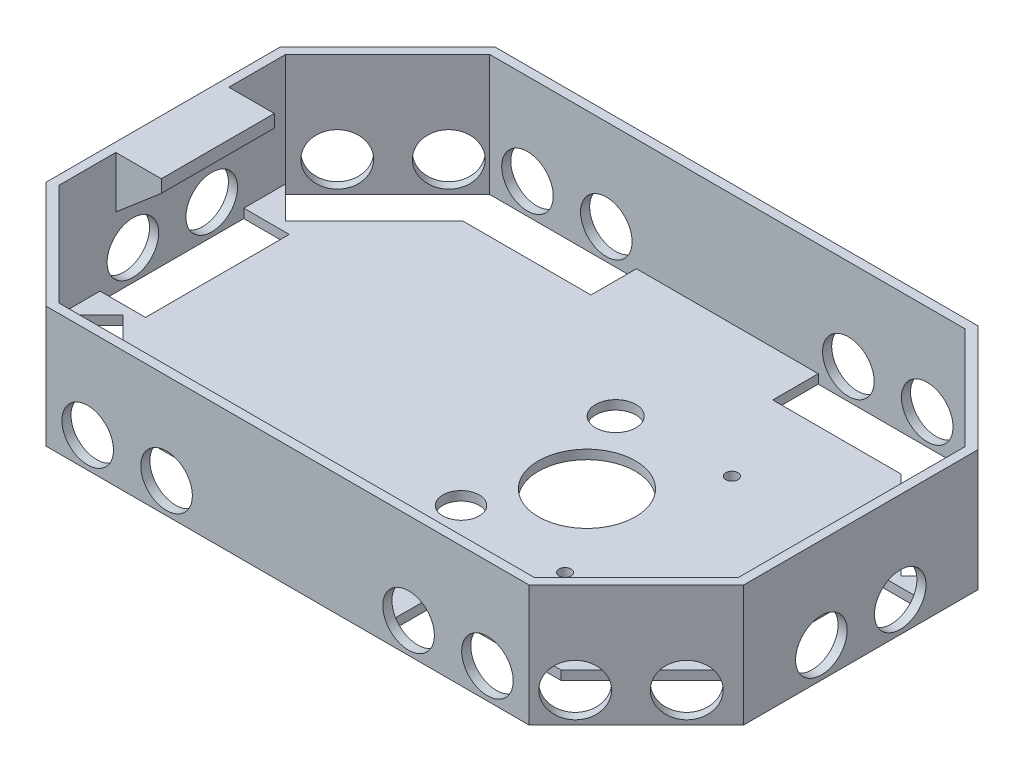
SolidWorks part; units mm, degrees
ref_plane "Front Plane" through (0, 0, 0) normal (0, 0, 1) x (1, 0, 0)
ref_plane "Top Plane" through (0, 0, 0) normal (0, 1, 0) x (1, 0, 0)
ref_plane "Right Plane" through (0, 0, 0) normal (1, 0, 0) x (0, 0, -1)
sketch "Sketch2" plane through (0, 0, 0) normal (0, 1, 0) x (1, 0, 0)
  line L0 (-115, 0) -> (115, 0) construction
  line L1 (-115, -74) -> (115, -74)
  line L2 (-115, -74) -> (-115, 74)
  line L3 (-115, 74) -> (115, 74)
  line L4 (115, -74) -> (115, 74)
  line L5 (-115, -74) -> (115, 74) construction
  line L6 (-115, 74) -> (115, -74) construction
  line L7 (-115, 74) -> (45, 74) construction
  line L8 (45, 74) -> (45, 0) construction
  circle A0 centre (45, 27.5) radius 2
  circle A1 centre (24.698, 0) radius 16
  circle A2 centre (8.698, 25.5) radius 6
  circle A3 centre (45, -27.5) radius 2
  circle A4 centre (8.698, -25.5) radius 6
  point P0 (0, 0)
  point P8 (45, 27.5)
  dimension "D1" = 230
  dimension "D2" = 148
  dimension "D3" = 160
  dimension "D4" = 27.5
extrude "Boss-Extrude1" add sketch "Sketch2" along normal blind 40 contours L2 L1 L4 L3
sketch "Sketch4" plane through (0, 40, 0) normal (0, 1, 0) x (1, 0, 0)
  line L0 (-79.6447, 74) -> (-115, 38.6447)
  line L1 (115, 74) -> (-115, 74) construction
  line L2 (-115, 74) -> (-115, -74) construction
  line L3 (-115, 38.6447) -> (-115, 74)
  line L4 (-115, 74) -> (-79.6447, 74)
  line L5 (-115, 0) -> (115, 0) construction
  line L6 (115, -74) -> (115, 74) construction
  line L7 (115, 0) -> (0, 0) construction
  line L8 (0, 0) -> (0, 74) construction
  line L9 (0, 74) -> (0, -74) construction
  line L10 (-115, -74) -> (115, -74) construction
  line L11 (115, 74) -> (79.6447, 74)
  line L12 (115, 38.6447) -> (115, 74)
  line L13 (79.6447, 74) -> (115, 38.6447)
  line L14 (115, -38.6447) -> (115, -74)
  line L15 (115, -74) -> (79.6447, -74)
  line L16 (79.6447, -74) -> (115, -38.6447)
  line L17 (-115, -74) -> (-79.6447, -74)
  line L18 (-115, -38.6447) -> (-115, -74)
  line L19 (-79.6447, -74) -> (-115, -38.6447)
  dimension "D1" = 50
  dimension "D2" = 159.2893
  dimension "D3" = 77.2893
  dimension "D4" = 230
  dimension "D5" = 148
extrude "Cut-Extrude2" cut sketch "Sketch4" against normal blind 126
shell "Shell2" thickness 3
sketch "Sketch6" plane through (0, 0, 0) normal (0, -1, 0) x (1, 0, 0)
  circle A0 centre (24.698, 0) radius 16
  circle A1 centre (8.698, 25.5) radius 6
  circle A2 centre (45, 27.5) radius 2
  circle A3 centre (8.698, -25.5) radius 6.6581
  circle A4 centre (45, -27.5) radius 2.011
extrude "Cut-Extrude3" cut sketch "Sketch6" against normal blind 126
sketch "Sketch8" plane through (0, 3, 0) normal (0, 1, 0) x (1, 0, 0)
  line L0 (-78.402, 71) -> (78.402, 71) construction
  line L1 (0, 71) -> (0, -71) construction
  line L2 (-75.9393, 71) -> (-29.9737, 71)
  line L4 (-72.1888, 56) -> (-29.9737, 56)
  line L5 (-29.9737, 71) -> (-29.9737, 56)
  line L6 (-78.402, -71) -> (78.402, -71) construction
  line L11 (-115, 0) -> (104.5294, 0) construction
  line L12 (-115, 0) -> (115, 0) construction
  line L21 (112, -37.402) -> (112, 37.402) construction
  line L22 (112, 23.5674) -> (97, 23.5674)
  line L23 (112, 23.5674) -> (112, -23.8324)
  line L24 (112, -23.8324) -> (97, -23.8324)
  line L25 (97, 23.5674) -> (97, -23.8324)
  line L26 (-112, -23.8324) -> (-97, -23.8324)
  line L27 (-97, 23.5674) -> (-97, -23.8324)
  line L28 (-112, 23.5674) -> (-97, 23.5674)
  line L29 (-112, 23.5674) -> (-112, -23.8324)
  line L30 (-78.402, 71) -> (-112, 37.402)
  line L31 (-112, 37.402) -> (-101.3934, 26.7954)
  line L32 (-101.3934, 26.7954) -> (-72.1888, 56)
  line L33 (-78.402, 71) -> (-75.9393, 71)
  line L34 (101.3934, 26.7954) -> (72.1888, 56)
  line L35 (112, 37.402) -> (101.3934, 26.7954)
  line L36 (78.402, 71) -> (112, 37.402)
  line L37 (78.402, 71) -> (75.9393, 71)
  line L38 (75.9393, 71) -> (29.9737, 71)
  line L39 (29.9737, 71) -> (29.9737, 56)
  line L40 (72.1888, 56) -> (29.9737, 56)
  line L41 (112, -37.402) -> (101.3934, -26.7954)
  line L42 (78.402, -71) -> (112, -37.402)
  line L43 (78.402, -71) -> (75.9393, -71)
  line L44 (75.9393, -71) -> (29.9737, -71)
  line L45 (29.9737, -71) -> (29.9737, -56)
  line L46 (72.1888, -56) -> (29.9737, -56)
  line L47 (101.3934, -26.7954) -> (72.1888, -56)
  line L48 (-101.3934, -26.7954) -> (-72.1888, -56)
  line L49 (-112, -37.402) -> (-101.3934, -26.7954)
  line L50 (-78.402, -71) -> (-112, -37.402)
  line L51 (-78.402, -71) -> (-75.9393, -71)
  line L52 (-75.9393, -71) -> (-29.9737, -71)
  line L53 (-29.9737, -71) -> (-29.9737, -56)
  line L54 (-72.1888, -56) -> (-29.9737, -56)
  point P0 (-75.9393, 71)
  point P1 (-29.9737, 71)
  dimension "D2" = 15
extrude "Cut-Extrude4" cut sketch "Sketch8" against normal blind 10
sketch "Sketch10" plane through (0, 0, -74) normal (0, 0, -1) x (-1, 0, 0)
  line L0 (0, 0) -> (0, 40) construction
  line L1 (79.6447, 0) -> (-79.6447, 0) construction
  line L2 (79.6447, 40) -> (-79.6447, 40) construction
  circle A0 centre (-65.902, 10) radius 8.5
  circle A1 centre (-39.902, 10) radius 8.5
  circle A2 centre (39.902, 10) radius 8.5
  circle A3 centre (65.902, 10) radius 8.5
sketch "Sketch12" plane through (0, 0, 74) normal (0, 0, 1) x (1, 0, 0)
  circle A0 centre (-65.902, 10) radius 8.5
  circle A1 centre (-39.902, 10) radius 8.5
  circle A2 centre (39.902, 10) radius 8.5
  circle A3 centre (65.902, 10) radius 8.5
extrude "Cut-Extrude7" cut sketch "Sketch12" along normal blind 4 and the other way blind 13
sketch "Sketch13" plane through (0, 0, -74) normal (0, 0, -1) x (-1, 0, 0)
  circle A0 centre (-39.902, 10) radius 8.5
  circle A1 centre (-65.902, 10) radius 8.5
  circle A2 centre (39.902, 10) radius 8.5
  circle A3 centre (65.902, 10) radius 8.5
extrude "Cut-Extrude8" cut sketch "Sketch13" against normal blind 10
sketch "Sketch14" plane through (-115, 0, 0) normal (-1, 0, 0) x (0, 0, 1)
  circle A0 centre (12.998, 10) radius 8.5
  circle A1 centre (-13.002, 10) radius 8.5
extrude "Cut-Extrude9" cut sketch "Sketch14" against normal blind 10
sketch "Sketch15" plane through (-76.8223, 0, -76.8223) normal (-0.7071, 0, -0.7071) x (-0.7071, 0, 0.7071)
  circle A0 centre (14.734, 10) radius 8.5
  circle A1 centre (40.734, 10) radius 8.5
extrude "Cut-Extrude10" cut sketch "Sketch15" against normal blind 10
sketch "Sketch16" plane through (-76.8223, 0, 76.8223) normal (-0.7071, 0, 0.7071) x (0.7071, 0, 0.7071)
  circle A0 centre (-40.734, 10) radius 8.5
  circle A1 centre (-14.734, 10) radius 8.5
extrude "Cut-Extrude11" cut sketch "Sketch16" against normal blind 10
sketch "Sketch17" plane through (115, 0, 0) normal (1, 0, 0) x (0, 0, -1)
  circle A0 centre (13.002, 10) radius 8.5
  circle A1 centre (-12.998, 10) radius 8.5
extrude "Cut-Extrude12" cut sketch "Sketch17" against normal blind 10
sketch "Sketch18" plane through (76.8223, 0, 76.8223) normal (0.7071, 0, 0.7071) x (0.7071, 0, -0.7071)
  circle A0 centre (40.734, 10) radius 8.5
  circle A1 centre (14.734, 10) radius 8.5
extrude "Cut-Extrude13" cut sketch "Sketch18" against normal blind 10
sketch "Sketch19" plane through (76.8223, 0, -76.8223) normal (0.7071, 0, -0.7071) x (-0.7071, 0, -0.7071)
  circle A0 centre (-40.734, 10) radius 8.5
  circle A1 centre (-14.734, 10) radius 8.5
extrude "Cut-Extrude14" cut sketch "Sketch19" against normal blind 10
sketch "Sketch23" plane through (-112, 0, 0) normal (1, 0, 0) x (0, 0, -1)
  line L8 (-18.6263, 35.8087) -> (-18.6263, 40)
  line L9 (-18.6263, 35.8087) -> (18.6263, 35.8087)
  line L10 (-18.6263, 40) -> (18.6263, 40)
  line L11 (18.6263, 35.8087) -> (18.6263, 40)
  line L12 (-18.6263, 35.8087) -> (18.6263, 40) construction
  line L13 (-18.6263, 40) -> (18.6263, 35.8087) construction
  point P1 (0, 33.6075)
  point P2 (0, 35.9028)
  point P3 (0, 37.9044)
extrude "Boss-Extrude2" add sketch "Sketch23" along normal blind 15
sketch "Sketch26" plane through (0, 0, 18.6263) normal (0, 0, 1) x (1, 0, 0)
  line L0 (-112.2324, 35.8087) -> (-112.2324, 22.8166)
  line L1 (-112.2324, 22.8166) -> (-97, 35.8087)
  line L2 (-97, 35.8087) -> (-112.2324, 35.8087)
  line L3 (-97, 35.8087) -> (-112, 35.8087) construction
extrude "Boss-Extrude3" add sketch "Sketch26" against normal up to surface (37.2526 mm away) up to face at (-104.5, 37.9044, -18.6263)
